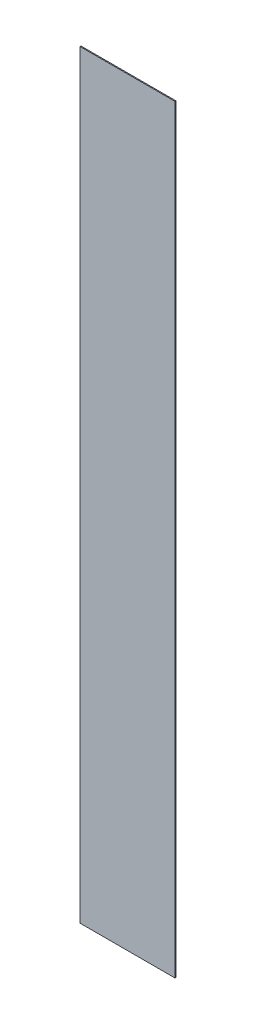
SolidWorks part; units mm, degrees
ref_plane "Front Plane" through (0, 0, 0) normal (0, 0, 1) x (1, 0, 0)
ref_plane "Top Plane" through (0, 0, 0) normal (0, 1, 0) x (1, 0, 0)
ref_plane "Right Plane" through (0, 0, 0) normal (1, 0, 0) x (0, 0, -1)
sketch "Sketch1" plane through (0, 0, 0) normal (0, 0, 1) x (1, 0, 0)
  line L1 (0, 0) -> (50.8, 0)
  line L2 (0, 0) -> (0, 406.4)
  line L3 (0, 406.4) -> (50.8, 406.4)
  line L4 (50.8, 0) -> (50.8, 406.4)
  dimension "D1" = 406.4
  dimension "D2" = 50.8
extrude "Boss-Extrude1" add sketch "Sketch1" along normal blind 0.508
